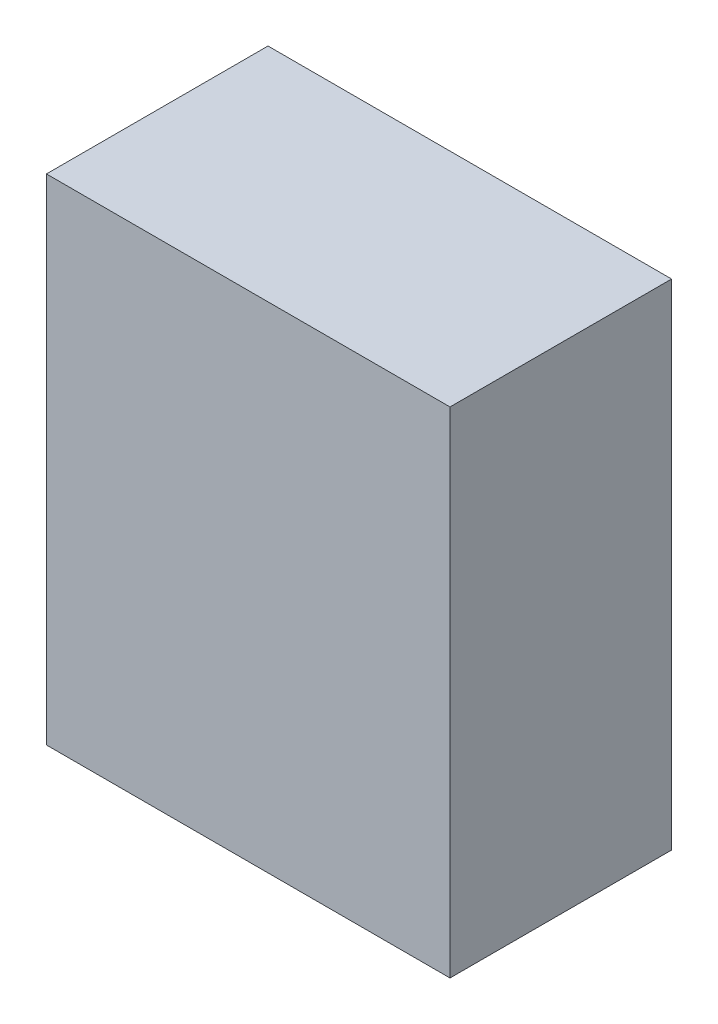
SolidWorks part; units mm, degrees
ref_plane "Front Plane" through (0, 0, 0) normal (0, 0, 1) x (1, 0, 0)
ref_plane "Top Plane" through (0, 0, 0) normal (0, 1, 0) x (1, 0, 0)
ref_plane "Right Plane" through (0, 0, 0) normal (1, 0, 0) x (0, 0, -1)
sketch "Sketch1" plane through (0, 0, 0) normal (0, 0, 1) x (1, 0, 0)
  line L1 (-25.5, 31.25) -> (25.5, 31.25)
  line L2 (-25.5, 31.25) -> (-25.5, -31.25)
  line L3 (-25.5, -31.25) -> (25.5, -31.25)
  line L4 (25.5, 31.25) -> (25.5, -31.25)
  line L5 (-25.5, 31.25) -> (25.5, -31.25) construction
  line L6 (-25.5, -31.25) -> (25.5, 31.25) construction
  point P0 (0, 0)
  dimension "D1" = 62.5
  dimension "D2" = 51
extrude "Boss-Extrude1" add sketch "Sketch1" along normal blind 28
